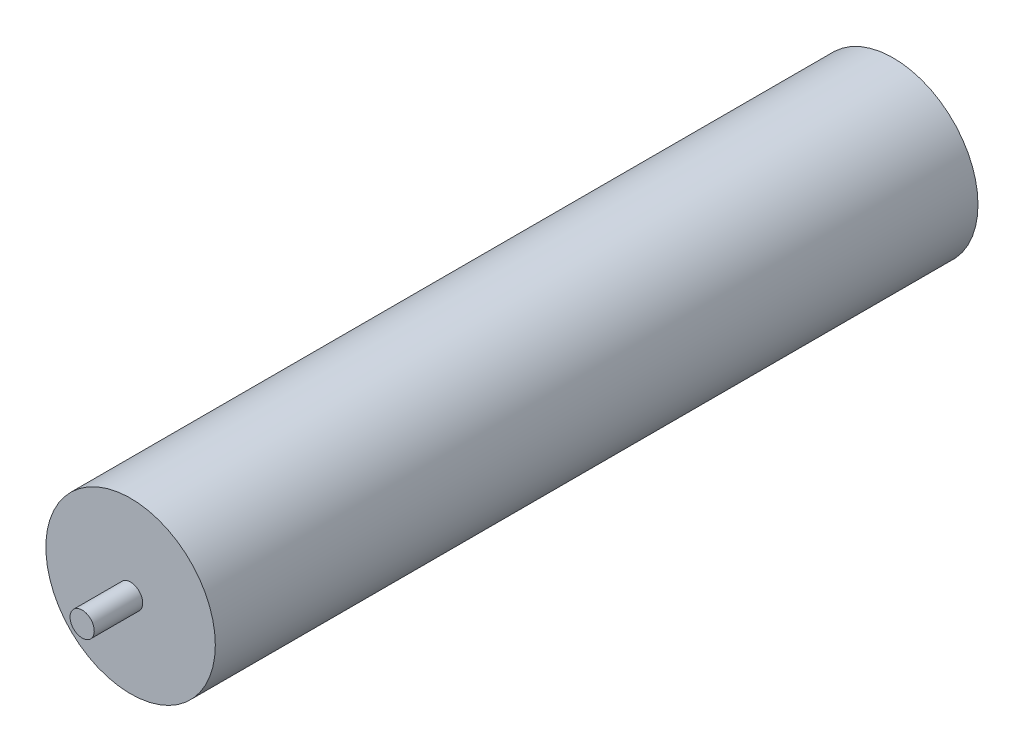
SolidWorks part; units mm, degrees
ref_plane "Front Plane" through (0, 0, 0) normal (0, 0, 1) x (1, 0, 0)
ref_plane "Top Plane" through (0, 0, 0) normal (0, 1, 0) x (1, 0, 0)
ref_plane "Right Plane" through (0, 0, 0) normal (1, 0, 0) x (0, 0, -1)
sketch "Sketch1" plane through (0, 0, 0) normal (0, 0, 1) x (1, 0, 0)
  circle A0 centre (0, 0) radius 35
  dimension "D1" = 70
extrude "Boss-Extrude1" add sketch "Sketch1" along normal blind 315
sketch "Sketch2" plane through (0, 0, 315) normal (0, 0, 1) x (1, 0, 0)
  circle A0 centre (0, 0) radius 5
  dimension "D1" = 10
extrude "Boss-Extrude2" add sketch "Sketch2" along normal blind 20
sketch "Sketch3" plane through (0, 0, 0) normal (0, 0, -1) x (-1, 0, 0)
  circle A0 centre (0, 0) radius 5
  dimension "D1" = 10
extrude "Boss-Extrude3" add sketch "Sketch3" along normal blind 20
